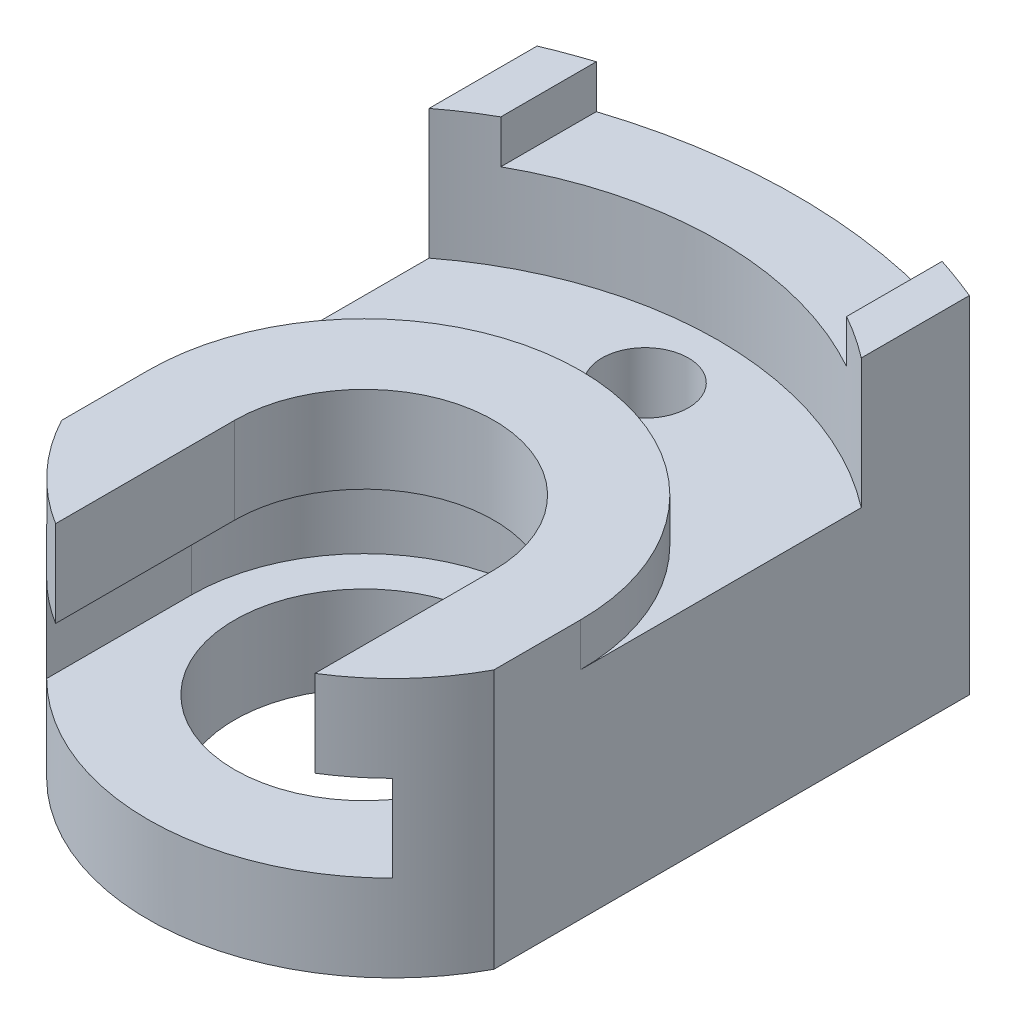
SolidWorks part; units mm, degrees
ref_plane "Front" through (0, 0, 0) normal (0, 0, 1) x (1, 0, 0)
ref_plane "Top" through (0, 0, 0) normal (0, 1, 0) x (1, 0, 0)
ref_plane "Right" through (0, 0, 0) normal (1, 0, 0) x (0, 0, -1)
sketch "Sketch1" plane through (0, 0, 0) normal (0, 0, 1) x (1, 0, 0)
  line L1 (-5, -4) -> (5, -4)
  line L2 (-5, -4) -> (-5, 4)
  line L3 (-5, 4) -> (5, 4)
  line L4 (5, -4) -> (5, 4)
  line L5 (-5, -4) -> (5, 4) construction
  line L6 (-5, 4) -> (5, -4) construction
  line L7 (-4, 3) -> (4, 3)
  line L8 (-4, 3) -> (-4, 5)
  line L9 (-4, 5) -> (4, 5)
  line L10 (4, 3) -> (4, 5)
  point P0 (0, 0)
  dimension "D1" = 10
  dimension "D2" = 8
  dimension "D3" = 7
  dimension "D4" = 1
  dimension "D5" = 1
  dimension "D6" = 2
extrude "Boss-Extrude1" add sketch "Sketch1" along normal mid plane 15 contours L10 L7 L8 L3 L2 L1 L4
sketch "Sketch2" plane through (0, 4, 0) normal (0, 1, 0) x (1, 0, 0)
  line L0 (-5, -7.5) -> (-5, 7.5) construction
  line L1 (5, -7.5) -> (5, 7.5) construction
  line L2 (-4, 7.5) -> (4, 7.5) construction
  line L3 (-5, 6.5) -> (-5, 7.5)
  line L4 (-5, 7.5) -> (5, 7.5)
  line L5 (5, 7.5) -> (5, 6.5)
  line L6 (-4, -7.5) -> (4, -7.5) construction
  line L7 (-5, -4.5) -> (-5, -7.5)
  line L8 (-5, -7.5) -> (5, -7.5)
  line L9 (5, -7.5) -> (5, -4.5)
  arc A0 (-5, 6.5) -> (5, 6.5) centre (0, -5.5) cw
  arc A1 (-5, -4.5) -> (5, -4.5) centre (0, -1.8333) ccw
  circle A2 centre (0, 4) radius 0.5
  circle A3 centre (0, -2.5) radius 3
  line M2 (5, 7.5) -> (4, 7.5)
  line M3 (4, 7.5) -> (4, -7.5)
  line M4 (4, -7.5) -> (5, -7.5)
  line M5 (5, -7.5) -> (5, 7.5)
  dimension "D5" = 1
  dimension "D7" = 6
  dimension "D1" = 1
  dimension "D2" = 1
  dimension "D3" = 3
  dimension "D4" = 3
  dimension "D6" = 3.5
  dimension "D8" = 5
extrude "Cut-Extrude1" cut sketch "Sketch2" against normal blind 15 contours L3 A0 L4 | L4 A0 M3 | A0 M3 M5 M2 | A2 | A1 L7 L8 | A1 M3 M4 M5 | A1 L8 M3 | A3
sketch "Sketch4" plane through (0, 3, 0) normal (0, 1, 0) x (1, 0, 0)
  line L0 (0, -2.5) -> (0, -9.1881) construction
  line L1 (3, -2.5) -> (3, -9.1881)
  line L2 (-3, -2.5) -> (-3, -9.1881)
  arc A0 (3, -2.5) -> (-3, -2.5) centre (0, -2.5) ccw
  arc A1 (-3, -9.1881) -> (3, -9.1881) centre (0, -9.1881) ccw
  point P4 (0, -5.844)
  dimension "D1" = 3
extrude "Cut-Extrude2" cut sketch "Sketch4" against normal blind 3
sketch "Sketch5" plane through (0, 0, 0) normal (0, 1, 0) x (1, 0, 0)
  line L0 (0, -2.5) -> (0, -8.4759) construction
  line L1 (4, -2.5) -> (4, -8.4759)
  line L2 (-4, -2.5) -> (-4, -8.4759)
  arc A0 (4, -2.5) -> (-4, -2.5) centre (0, -2.5) ccw
  arc A1 (-4, -8.4759) -> (4, -8.4759) centre (0, -8.4759) ccw
  point P3 (0, -5.4879)
  dimension "D1" = 4
extrude "Cut-Extrude3" cut sketch "Sketch5" against normal blind 2
sketch "Sketch6" plane through (0, 4, 0) normal (0, 1, 0) x (1, 0, 0)
  line L0 (0, -2.5) -> (0, -8.5364) construction
  line L1 (5, -2.5) -> (5, -8.5364)
  line L2 (-5, -2.5) -> (-5, -8.5364)
  arc A0 (5, -2.5) -> (-5, -2.5) centre (0, -2.5) ccw
  arc A1 (-5, -8.5364) -> (5, -8.5364) centre (0, -8.5364) ccw
  point P4 (0, -5.5182)
  dimension "D1" = 5
extrude "Cut-Extrude4" cut sketch "Sketch6" against normal blind 2
sketch "Sketch7" plane through (0, 4, 0) normal (0, 1, 0) x (1, 0, 0)
  line L0 (-5, -2.5) -> (-5, 6.5) construction
  line L1 (5, -2.5) -> (5, 6.5) construction
  line L2 (-5, -2.5) -> (-5, 4)
  line L3 (5, -2.5) -> (5, 4)
  arc A0 (-5, -2.5) -> (5, -2.5) centre (0, -2.5) cw
  arc A1 (5, -2.5) -> (4, 0.5) centre (0, -2.5) ccw construction
  arc A2 (5, -2.5) -> (-5, -2.5) centre (0, -2.5) ccw construction
  arc A3 (-5, 4) -> (5, 4) centre (0, -2.5) cw
extrude "Cut-Extrude5" cut sketch "Sketch7" against normal blind 3
sketch "Sketch8" plane through (0, 1, 0) normal (0, 1, 0) x (1, 0, 0)
  circle A0 centre (0, 4) radius 1
  dimension "D1" = 2
extrude "Cut-Extrude6" cut sketch "Sketch8" against normal blind 2
